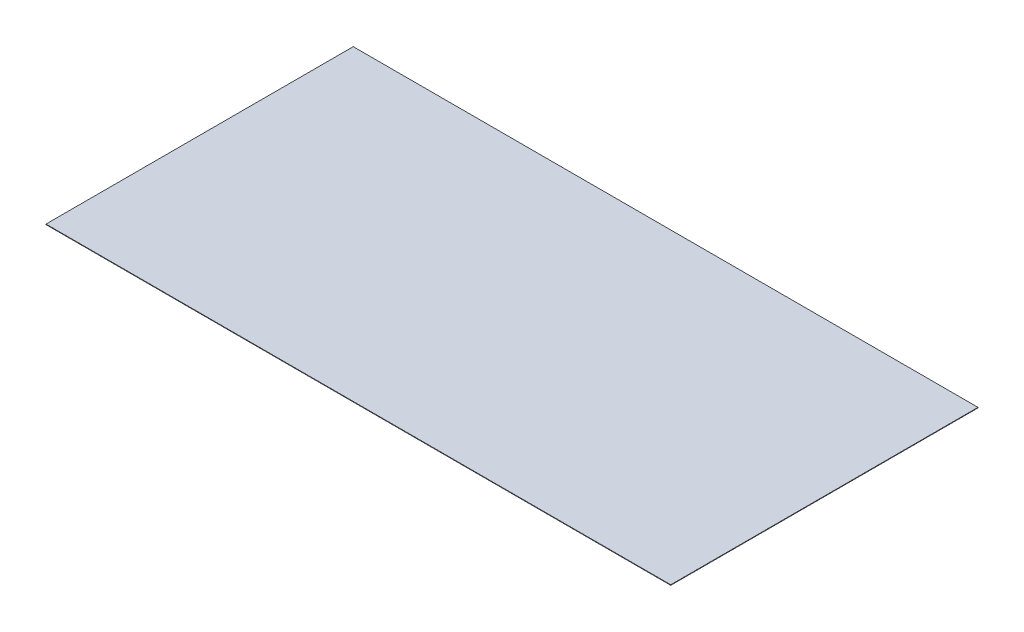
SolidWorks part; units mm, degrees
material "Plain Carbon Steel"
ref_plane "Front Plane" through (0, 0, 0) normal (0, 0, 1) x (1, 0, 0)
ref_plane "Top Plane" through (0, 0, 0) normal (0, 1, 0) x (1, 0, 0)
ref_plane "Right Plane" through (0, 0, 0) normal (1, 0, 0) x (0, 0, -1)
sketch "Sketch1" plane through (0, 0, 0) normal (0, 1, 0) x (1, 0, 0)
  line L1 (-1220, -600) -> (1220, -600)
  line L2 (-1220, -600) -> (-1220, 600)
  line L3 (-1220, 600) -> (1220, 600)
  line L4 (1220, -600) -> (1220, 600)
  line L5 (-1220, -600) -> (1220, 600) construction
  line L6 (-1220, 600) -> (1220, -600) construction
  point P0 (0, 0)
  dimension "D1" = 2440
  dimension "D2" = 1200
extrude "Boss-Extrude1" add sketch "Sketch1" along normal blind 2
